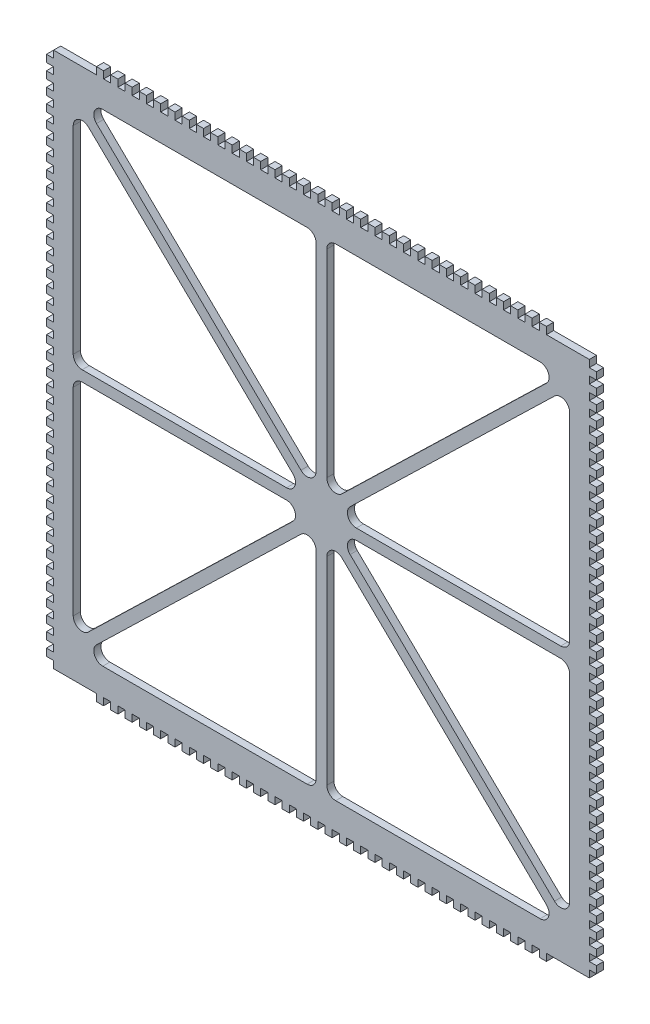
SolidWorks part; units mm, degrees
material "Cedar"
ref_plane "Front Plane" through (0, 0, 0) normal (0, 0, 1) x (1, 0, 0)
ref_plane "Top Plane" through (0, 0, 0) normal (0, 1, 0) x (1, 0, 0)
ref_plane "Right Plane" through (0, 0, 0) normal (1, 0, 0) x (0, 0, -1)
sketch "Sketch1" plane through (0, 0, 0) normal (0, 0, 1) x (1, 0, 0)
  line L0 (0, 0) -> (0, 50) construction
  line L1 (0, 0) -> (-64, 0) construction
  line L2 (-154, -150) -> (-154, 150)
  line L3 (-154, 150) -> (154, 150)
  line L5 (-122.4771, 135) -> (-8, 135)
  line L6 (5.0873, -5.1548) -> (7.1745, -3) construction
  line L7 (154, -150) -> (154, 150)
  line L8 (-154, -150) -> (154, -150)
  line L9 (3, -7.3097) -> (5.0873, -5.1548) construction
  line L10 (-130.5212, 122.4775) -> (-16.0442, 11.5914)
  line L11 (-19.5229, 3) -> (-134, 3)
  line L12 (8, 135) -> (122.4771, 135)
  line L13 (-125.9558, 126.4086) -> (-11.4788, 15.5225)
  line L14 (-3, 19.1139) -> (-3, 130)
  line L15 (64.5173, 58.544) -> (60.3428, 62.8537) construction
  line L16 (3, 130) -> (3, 19.1139)
  line L17 (11.4788, 15.5225) -> (125.9558, 126.4086)
  line L18 (62.4301, 60.6989) -> (90.4185, 87.8094) construction
  line L19 (130.5212, 122.4775) -> (16.0442, 11.5914)
  line L20 (19.5229, 3) -> (134, 3)
  line L21 (134.8255, 135) -> (136.9127, 132.8452) construction
  line L22 (136.9127, 132.8452) -> (139, 130.6903) construction
  line L23 (-76.0173, 78.0365) -> (-80.1918, 73.7268) construction
  line L24 (-80.1918, 73.7268) -> (-78.1045, 75.8817) construction
  line L25 (-78.1045, 75.8817) -> (-90.4799, 87.8689) construction
  line L26 (-134.8255, 135) -> (-136.9127, 132.8452) construction
  line L27 (-136.9127, 132.8452) -> (-139, 130.6903) construction
  line L28 (9.2327, -9.1702) -> (4.4592, -4.5465) construction
  line L29 (7.1454, -11.3251) -> (11.3199, -7.0154) construction
  line L30 (-5.0873, -5.1548) -> (-7.1745, -3) construction
  line L31 (-3, -7.3097) -> (-5.0873, -5.1548) construction
  line L32 (-10.1915, -10.099) -> (-3.6148, -3.7286) construction
  line L33 (-12.2788, -7.9441) -> (-10.1915, -10.099) construction
  line L34 (-8.1042, -12.2538) -> (-12.2788, -7.9441) construction
  line L35 (-136.9127, -132.8452) -> (-139, -130.6903) construction
  line L36 (-134.8255, -135) -> (-136.9127, -132.8452) construction
  line L37 (-80.1918, -73.7268) -> (-78.1045, -75.8817) construction
  line L38 (-76.0173, -78.0365) -> (-80.1918, -73.7268) construction
  line L39 (136.9127, -132.8452) -> (139, -130.6903) construction
  line L40 (134.8255, -135) -> (136.9127, -132.8452) construction
  line L41 (64.5173, -58.544) -> (60.3428, -62.8537) construction
  line L42 (-139, -8) -> (-139, -118.8861)
  line L43 (139, -8) -> (139, -118.8861)
  line L44 (19.5229, -3) -> (134, -3)
  line L45 (130.5212, -122.4775) -> (16.0442, -11.5914)
  line L46 (139, 8) -> (139, 118.8861)
  line L47 (-139, 8) -> (-139, 118.8861)
  line L48 (-8.1042, 12.2538) -> (-12.2788, 7.9441) construction
  line L49 (-12.2788, 7.9441) -> (-10.1915, 10.099) construction
  line L50 (-10.1915, 10.099) -> (-3.6148, 3.7286) construction
  line L51 (-3, 7.3097) -> (-5.0873, 5.1548) construction
  line L52 (-5.0873, 5.1548) -> (-7.1745, 3) construction
  line L53 (7.1454, 11.3251) -> (11.3199, 7.0154) construction
  line L54 (9.2327, 9.1702) -> (4.4592, 4.5465) construction
  line L55 (3, 7.3097) -> (5.0873, 5.1548) construction
  line L56 (5.0873, 5.1548) -> (7.1745, 3) construction
  line L57 (11.4788, -15.5225) -> (125.9558, -126.4086)
  line L58 (3, -130) -> (3, -19.1139)
  line L59 (-3, -19.1139) -> (-3, -130)
  line L60 (-125.9558, -126.4086) -> (-11.4788, -15.5225)
  line L61 (8, -135) -> (122.4771, -135)
  line L62 (-19.5229, -3) -> (-134, -3)
  line L63 (-130.5212, -122.4775) -> (-16.0442, -11.5914)
  line L64 (-122.4771, -135) -> (-8, -135)
  arc A0 (130.5212, 122.4775) -> (139, 118.8861) centre (134, 118.8861) cw
  arc A1 (134, 3) -> (139, 8) centre (134, 8) ccw
  arc A2 (16.0442, 11.5914) -> (19.5229, 3) centre (19.5229, 8) ccw
  arc A3 (3, 19.1139) -> (11.4788, 15.5225) centre (8, 19.1139) ccw
  arc A4 (125.9558, 126.4086) -> (122.4771, 135) centre (122.4771, 130) ccw
  arc A5 (3, 130) -> (8, 135) centre (8, 130) cw
  arc A6 (-125.9558, 126.4086) -> (-122.4771, 135) centre (-122.4771, 130) cw
  arc A7 (-11.4788, 15.5225) -> (-3, 19.1139) centre (-8, 19.1139) ccw
  arc A8 (-3, 130) -> (-8, 135) centre (-8, 130) ccw
  arc A9 (-16.0442, 11.5914) -> (-19.5229, 3) centre (-19.5229, 8) cw
  arc A10 (-139, 8) -> (-134, 3) centre (-134, 8) ccw
  arc A11 (-130.5212, 122.4775) -> (-139, 118.8861) centre (-134, 118.8861) ccw
  arc A12 (-130.5212, -122.4775) -> (-139, -118.8861) centre (-134, -118.8861) cw
  arc A13 (-139, -8) -> (-134, -3) centre (-134, -8) cw
  arc A14 (-16.0442, -11.5914) -> (-19.5229, -3) centre (-19.5229, -8) ccw
  arc A15 (-3, -130) -> (-8, -135) centre (-8, -130) cw
  arc A16 (-11.4788, -15.5225) -> (-3, -19.1139) centre (-8, -19.1139) cw
  arc A17 (-125.9558, -126.4086) -> (-122.4771, -135) centre (-122.4771, -130) ccw
  arc A18 (3, -130) -> (8, -135) centre (8, -130) ccw
  arc A19 (125.9558, -126.4086) -> (122.4771, -135) centre (122.4771, -130) cw
  arc A20 (3, -19.1139) -> (11.4788, -15.5225) centre (8, -19.1139) cw
  arc A21 (16.0442, -11.5914) -> (19.5229, -3) centre (19.5229, -8) cw
  arc A22 (134, -3) -> (139, -8) centre (134, -8) cw
  arc A23 (130.5212, -122.4775) -> (139, -118.8861) centre (134, -118.8861) ccw
  point P19 (0, 83)
  point P21 (0, 150)
  point P27 (-64, 0)
  point P28 (64, 0)
  point P29 (87, 0)
  point P34 (-87, 0)
  point P76 (139, 3)
  point P88 (3, 135)
  point P97 (-3, 135)
  point P103 (-139, 3)
  point P144 (-139, -3)
  point P145 (-3, -135)
  point P146 (3, -135)
  point P147 (139, -3)
  point P148 (0, -83)
  dimension "D3" = 15
  dimension "D8" = 150
  dimension "D7" = 6
  dimension "D9" = 6
  dimension "D10" = 3
  dimension "D11" = 150
  dimension "D12" = 5
  dimension "D2" = 308
  dimension "D4" = 15
  dimension "D5" = 3
  dimension "D6" = 3
  dimension "D13" = 15
extrude "Boss-Extrude1" add sketch "Sketch1" along normal blind 4
sketch "Sketch2" plane through (0, 0, 4) normal (0, 0, 1) x (1, 0, 0)
  line L0 (0, 0) -> (-89.2695, 0) construction
  line L1 (0, 0) -> (0, 71.1996) construction
  line L2 (-154, 2) -> (-150, 2)
  line L3 (-154, -150) -> (154, -150) construction
  line L4 (-154, -150) -> (-154, 150) construction
  line L5 (-154, 138) -> (-150, 138)
  line L6 (-154, 138) -> (-154, 142)
  line L7 (-154, 142) -> (-150, 142)
  line L8 (-150, 138) -> (-150, 142)
  line L9 (-154, 130) -> (-150, 130)
  line L10 (-154, 130) -> (-154, 134)
  line L11 (-154, 134) -> (-150, 134)
  line L12 (-150, 130) -> (-150, 134)
  line L13 (-154, 122) -> (-150, 122)
  line L14 (-154, 122) -> (-154, 126)
  line L15 (-154, 126) -> (-150, 126)
  line L16 (-150, 122) -> (-150, 126)
  line L17 (-154, 114) -> (-150, 114)
  line L18 (-154, 114) -> (-154, 118)
  line L19 (-154, 118) -> (-150, 118)
  line L20 (-150, 114) -> (-150, 118)
  line L21 (-154, 106) -> (-150, 106)
  line L22 (-154, 106) -> (-154, 110)
  line L23 (-154, 110) -> (-150, 110)
  line L24 (-150, 106) -> (-150, 110)
  line L25 (-154, 98) -> (-150, 98)
  line L26 (-154, 98) -> (-154, 102)
  line L27 (-154, 102) -> (-150, 102)
  line L28 (-150, 98) -> (-150, 102)
  line L29 (-154, 90) -> (-150, 90)
  line L30 (-154, 90) -> (-154, 94)
  line L31 (-154, 94) -> (-150, 94)
  line L32 (-150, 90) -> (-150, 94)
  line L33 (-154, 82) -> (-150, 82)
  line L34 (-154, 82) -> (-154, 86)
  line L35 (-154, 86) -> (-150, 86)
  line L36 (-150, 82) -> (-150, 86)
  line L37 (-154, 74) -> (-150, 74)
  line L38 (-154, 74) -> (-154, 78)
  line L39 (-154, 78) -> (-150, 78)
  line L40 (-150, 74) -> (-150, 78)
  line L41 (-154, 66) -> (-150, 66)
  line L42 (-154, 66) -> (-154, 70)
  line L43 (-154, 70) -> (-150, 70)
  line L44 (-150, 66) -> (-150, 70)
  line L45 (-154, 58) -> (-150, 58)
  line L46 (-154, 58) -> (-154, 62)
  line L47 (-154, 62) -> (-150, 62)
  line L48 (-150, 58) -> (-150, 62)
  line L49 (-154, 50) -> (-150, 50)
  line L50 (-154, 50) -> (-154, 54)
  line L51 (-154, 54) -> (-150, 54)
  line L52 (-150, 50) -> (-150, 54)
  line L53 (-154, 42) -> (-150, 42)
  line L54 (-154, 42) -> (-154, 46)
  line L55 (-154, 46) -> (-150, 46)
  line L56 (-150, 42) -> (-150, 46)
  line L57 (-154, 34) -> (-150, 34)
  line L58 (-154, 34) -> (-154, 38)
  line L59 (-154, 38) -> (-150, 38)
  line L60 (-150, 34) -> (-150, 38)
  line L61 (-154, 26) -> (-150, 26)
  line L62 (-154, 26) -> (-154, 30)
  line L63 (-154, 30) -> (-150, 30)
  line L64 (-150, 26) -> (-150, 30)
  line L65 (-154, 18) -> (-150, 18)
  line L66 (-154, 18) -> (-154, 22)
  line L67 (-154, 22) -> (-150, 22)
  line L68 (-150, 18) -> (-150, 22)
  line L69 (-154, 10) -> (-150, 10)
  line L70 (-154, 10) -> (-154, 14)
  line L71 (-154, 14) -> (-150, 14)
  line L72 (-150, 10) -> (-150, 14)
  line L73 (150, -142) -> (150, -138)
  line L74 (154, -138) -> (150, -138)
  line L75 (154, -142) -> (154, -138)
  line L76 (-150, -142) -> (-154, -142)
  line L77 (150, -134) -> (150, -130)
  line L78 (154, -130) -> (150, -130)
  line L79 (154, -134) -> (154, -130)
  line L80 (154, -134) -> (150, -134)
  line L81 (150, -126) -> (150, -122)
  line L82 (154, -122) -> (150, -122)
  line L83 (154, -126) -> (154, -122)
  line L84 (154, -126) -> (150, -126)
  line L85 (150, -118) -> (150, -114)
  line L86 (154, -114) -> (150, -114)
  line L87 (154, -118) -> (154, -114)
  line L88 (154, -118) -> (150, -118)
  line L89 (150, -110) -> (150, -106)
  line L90 (154, -106) -> (150, -106)
  line L91 (154, -110) -> (154, -106)
  line L92 (154, -110) -> (150, -110)
  line L93 (150, -102) -> (150, -98)
  line L94 (154, -98) -> (150, -98)
  line L95 (154, -102) -> (154, -98)
  line L96 (154, -102) -> (150, -102)
  line L97 (150, -94) -> (150, -90)
  line L98 (154, -90) -> (150, -90)
  line L99 (154, -94) -> (154, -90)
  line L100 (154, -94) -> (150, -94)
  line L101 (150, -86) -> (150, -82)
  line L102 (154, -82) -> (150, -82)
  line L103 (-154, 146) -> (-150, 146)
  line L104 (-154, 146) -> (-154, 150)
  line L105 (-154, 150) -> (-150, 150)
  line L106 (-150, 146) -> (-150, 150)
  line L107 (154, -86) -> (154, -82)
  line L108 (154, -86) -> (150, -86)
  line L109 (150, -78) -> (150, -74)
  line L110 (154, -74) -> (150, -74)
  line L111 (154, -78) -> (154, -74)
  line L112 (154, -78) -> (150, -78)
  line L113 (150, -70) -> (150, -66)
  line L114 (154, -66) -> (150, -66)
  line L115 (154, -70) -> (154, -66)
  line L116 (154, -70) -> (150, -70)
  line L117 (150, -62) -> (150, -58)
  line L118 (154, -58) -> (150, -58)
  line L119 (154, -62) -> (154, -58)
  line L120 (154, -62) -> (150, -62)
  line L121 (150, -54) -> (150, -50)
  line L122 (154, -50) -> (150, -50)
  line L123 (154, -54) -> (154, -50)
  line L124 (154, -54) -> (150, -54)
  line L125 (150, -46) -> (150, -42)
  line L126 (154, -42) -> (150, -42)
  line L127 (154, -46) -> (154, -42)
  line L128 (154, -46) -> (150, -46)
  line L129 (150, -38) -> (150, -34)
  line L130 (154, -34) -> (150, -34)
  line L131 (-154, 2) -> (-154, 6)
  line L132 (154, -38) -> (154, -34)
  line L133 (154, -38) -> (150, -38)
  line L134 (150, -30) -> (150, -26)
  line L135 (154, -26) -> (150, -26)
  line L136 (154, -30) -> (154, -26)
  line L137 (154, -30) -> (150, -30)
  line L138 (150, -22) -> (150, -18)
  line L139 (154, -18) -> (150, -18)
  line L140 (154, -22) -> (154, -18)
  line L141 (154, -22) -> (150, -22)
  line L142 (150, -14) -> (150, -10)
  line L143 (154, -10) -> (150, -10)
  line L144 (154, -14) -> (154, -10)
  line L145 (154, -14) -> (150, -14)
  line L146 (150, -6) -> (150, -2)
  line L147 (154, -2) -> (150, -2)
  line L148 (154, -6) -> (154, -2)
  line L149 (154, -6) -> (150, -6)
  line L150 (-154, 6) -> (-150, 6)
  line L151 (-150, 2) -> (-150, 6)
  line L152 (-154, -6) -> (-150, -6)
  line L153 (-154, -6) -> (-154, -2)
  line L154 (-154, -2) -> (-150, -2)
  line L155 (-150, -6) -> (-150, -2)
  line L156 (-154, -14) -> (-150, -14)
  line L157 (-154, -14) -> (-154, -10)
  line L158 (-154, -10) -> (-150, -10)
  line L159 (-150, -14) -> (-150, -10)
  line L160 (-154, -22) -> (-150, -22)
  line L161 (-154, -22) -> (-154, -18)
  line L162 (-154, -18) -> (-150, -18)
  line L163 (-150, -22) -> (-150, -18)
  line L164 (-154, -30) -> (-150, -30)
  line L165 (-154, -30) -> (-154, -26)
  line L166 (-154, -26) -> (-150, -26)
  line L167 (-150, -30) -> (-150, -26)
  line L168 (-154, -38) -> (-150, -38)
  line L169 (-154, -38) -> (-154, -34)
  line L170 (-154, -34) -> (-150, -34)
  line L171 (-150, -38) -> (-150, -34)
  line L172 (150, 2) -> (150, 6)
  line L173 (154, 6) -> (150, 6)
  line L174 (154, 2) -> (154, 6)
  line L175 (150, 146) -> (150, 150)
  line L176 (154, 150) -> (150, 150)
  line L177 (154, 146) -> (154, 150)
  line L178 (154, 146) -> (150, 146)
  line L179 (150, 10) -> (150, 14)
  line L180 (154, 14) -> (150, 14)
  line L181 (154, 10) -> (154, 14)
  line L182 (154, 10) -> (150, 10)
  line L183 (150, 18) -> (150, 22)
  line L184 (154, 22) -> (150, 22)
  line L185 (154, 18) -> (154, 22)
  line L186 (154, 18) -> (150, 18)
  line L187 (150, 26) -> (150, 30)
  line L188 (154, 30) -> (150, 30)
  line L189 (154, 26) -> (154, 30)
  line L190 (154, 26) -> (150, 26)
  line L191 (150, 34) -> (150, 38)
  line L192 (154, 38) -> (150, 38)
  line L193 (154, 34) -> (154, 38)
  line L194 (154, 34) -> (150, 34)
  line L195 (150, 42) -> (150, 46)
  line L196 (-154, -46) -> (-150, -46)
  line L197 (-154, -46) -> (-154, -42)
  line L198 (-154, -42) -> (-150, -42)
  line L199 (-150, -46) -> (-150, -42)
  line L200 (-154, -54) -> (-150, -54)
  line L201 (-154, -54) -> (-154, -50)
  line L202 (-154, -50) -> (-150, -50)
  line L203 (-150, -54) -> (-150, -50)
  line L204 (-154, -62) -> (-150, -62)
  line L205 (-154, -62) -> (-154, -58)
  line L206 (-154, -58) -> (-150, -58)
  line L207 (-150, -62) -> (-150, -58)
  line L208 (-154, -70) -> (-150, -70)
  line L209 (-154, -70) -> (-154, -66)
  line L210 (-154, -66) -> (-150, -66)
  line L211 (-150, -70) -> (-150, -66)
  line L212 (-154, -78) -> (-150, -78)
  line L213 (-154, -78) -> (-154, -74)
  line L214 (-154, -74) -> (-150, -74)
  line L215 (-150, -78) -> (-150, -74)
  line L216 (-154, -86) -> (-150, -86)
  line L217 (-154, -86) -> (-154, -82)
  line L218 (-154, -82) -> (-150, -82)
  line L219 (-150, -86) -> (-150, -82)
  line L220 (154, 46) -> (150, 46)
  line L221 (154, 42) -> (154, 46)
  line L222 (154, 42) -> (150, 42)
  line L223 (150, 50) -> (150, 54)
  line L224 (154, 54) -> (150, 54)
  line L225 (154, 50) -> (154, 54)
  line L226 (154, 50) -> (150, 50)
  line L227 (150, 58) -> (150, 62)
  line L228 (154, 62) -> (150, 62)
  line L229 (154, 58) -> (154, 62)
  line L230 (154, 58) -> (150, 58)
  line L231 (150, 66) -> (150, 70)
  line L232 (154, 70) -> (150, 70)
  line L233 (154, 66) -> (154, 70)
  line L234 (154, 66) -> (150, 66)
  line L235 (150, 74) -> (150, 78)
  line L236 (154, 78) -> (150, 78)
  line L237 (154, 74) -> (154, 78)
  line L238 (154, 74) -> (150, 74)
  line L239 (150, 82) -> (150, 86)
  line L240 (154, 86) -> (150, 86)
  line L241 (154, 82) -> (154, 86)
  line L242 (154, 82) -> (150, 82)
  line L243 (150, 90) -> (150, 94)
  line L244 (-154, -94) -> (-150, -94)
  line L245 (-154, -94) -> (-154, -90)
  line L246 (-154, -90) -> (-150, -90)
  line L247 (-150, -94) -> (-150, -90)
  line L248 (-154, -102) -> (-150, -102)
  line L249 (-154, -102) -> (-154, -98)
  line L250 (-154, -98) -> (-150, -98)
  line L251 (-150, -102) -> (-150, -98)
  line L252 (-154, -110) -> (-150, -110)
  line L253 (-154, -110) -> (-154, -106)
  line L254 (-154, -106) -> (-150, -106)
  line L255 (-150, -110) -> (-150, -106)
  line L256 (154, 94) -> (150, 94)
  line L257 (154, 90) -> (154, 94)
  line L258 (154, 90) -> (150, 90)
  line L259 (150, 98) -> (150, 102)
  line L260 (154, 102) -> (150, 102)
  line L261 (154, 98) -> (154, 102)
  line L262 (154, 98) -> (150, 98)
  line L263 (150, 106) -> (150, 110)
  line L264 (154, 110) -> (150, 110)
  line L265 (154, 106) -> (154, 110)
  line L266 (154, 106) -> (150, 106)
  line L267 (150, 114) -> (150, 118)
  line L268 (-154, -118) -> (-150, -118)
  line L269 (-154, -118) -> (-154, -114)
  line L270 (-154, -114) -> (-150, -114)
  line L271 (-150, -118) -> (-150, -114)
  line L272 (-154, -126) -> (-150, -126)
  line L273 (-154, -126) -> (-154, -122)
  line L274 (-154, -122) -> (-150, -122)
  line L275 (-150, -126) -> (-150, -122)
  line L276 (-154, -134) -> (-150, -134)
  line L277 (-154, -134) -> (-154, -130)
  line L278 (-154, -130) -> (-150, -130)
  line L279 (-150, -134) -> (-150, -130)
  line L280 (-154, -146) -> (-150, -146)
  line L281 (-154, -142) -> (-154, -138)
  line L282 (-154, -138) -> (-150, -138)
  line L283 (-150, -142) -> (-150, -138)
  line L284 (154, 118) -> (150, 118)
  line L285 (154, 114) -> (154, 118)
  line L286 (154, 114) -> (150, 114)
  line L287 (150, 122) -> (150, 126)
  line L288 (154, 126) -> (150, 126)
  line L289 (154, 122) -> (154, 126)
  line L290 (154, 122) -> (150, 122)
  line L291 (150, 130) -> (150, 134)
  line L292 (154, 134) -> (150, 134)
  line L293 (154, 130) -> (154, 134)
  line L294 (154, 130) -> (150, 130)
  line L295 (150, 138) -> (150, 142)
  line L296 (154, 142) -> (150, 142)
  line L297 (154, 138) -> (154, 142)
  line L298 (154, 138) -> (150, 138)
  line L299 (154, 2) -> (150, 2)
  line L300 (-154, 150) -> (154, 150) construction
  line L301 (-150, -146) -> (-150, -150)
  line L302 (-154, -150) -> (-154, -146)
  line L303 (-150, -150) -> (-154, -150)
  line L304 (150, -142) -> (154, -142)
  line L305 (150, -150) -> (154, -150)
  line L306 (150, -150) -> (150, -146)
  line L307 (150, -146) -> (154, -146)
  line L308 (154, -150) -> (154, 150) construction
  line L309 (-154, -142) -> (-150, -142) [skipped]
  line L310 (154, -146) -> (154, -150)
  dimension "D1" = 4
  dimension "D2" = 4
  dimension "D3" = 4
  dimension "D4" = 37
  dimension "D5" = 4
extrude "Cut-Extrude1" cut sketch "Sketch2" against normal blind 4
sketch "Sketch3" plane through (0, 0, 4) normal (0, 0, 1) x (1, 0, 0)
  line L0 (0, 150) -> (0, 114.5296) construction
  line L1 (-154, 150) -> (154, 150) construction
  line L2 (-10, 150) -> (-14, 150)
  line L3 (-2, 150) -> (-6, 150)
  line L4 (-2, 150) -> (-2, 154)
  line L5 (-2, 154) -> (-6, 154)
  line L6 (-6, 150) -> (-6, 154)
  line L7 (-10, 150) -> (-10, 154)
  line L8 (-10, 154) -> (-14, 154)
  line L9 (-14, 150) -> (-14, 154)
  line L10 (-18, 150) -> (-22, 150)
  line L11 (-18, 150) -> (-18, 154)
  line L12 (-18, 154) -> (-22, 154)
  line L13 (-22, 150) -> (-22, 154)
  line L14 (-26, 150) -> (-30, 150)
  line L15 (-26, 150) -> (-26, 154)
  line L16 (-26, 154) -> (-30, 154)
  line L17 (-30, 150) -> (-30, 154)
  line L18 (-34, 150) -> (-38, 150)
  line L19 (-34, 150) -> (-34, 154)
  line L20 (-34, 154) -> (-38, 154)
  line L21 (-38, 150) -> (-38, 154)
  line L22 (-42, 150) -> (-46, 150)
  line L23 (-42, 150) -> (-42, 154)
  line L24 (-42, 154) -> (-46, 154)
  line L25 (-46, 150) -> (-46, 154)
  line L26 (-50, 150) -> (-54, 150)
  line L27 (-50, 150) -> (-50, 154)
  line L28 (-50, 154) -> (-54, 154)
  line L29 (-54, 150) -> (-54, 154)
  line L30 (-58, 150) -> (-62, 150)
  line L31 (-58, 150) -> (-58, 154)
  line L32 (-58, 154) -> (-62, 154)
  line L33 (-62, 150) -> (-62, 154)
  line L34 (-66, 150) -> (-70, 150)
  line L35 (-66, 150) -> (-66, 154)
  line L36 (-66, 154) -> (-70, 154)
  line L37 (-70, 150) -> (-70, 154)
  line L38 (-74, 150) -> (-78, 150)
  line L39 (-74, 150) -> (-74, 154)
  line L40 (-74, 154) -> (-78, 154)
  line L41 (-78, 150) -> (-78, 154)
  line L42 (-82, 150) -> (-86, 150)
  line L43 (-82, 150) -> (-82, 154)
  line L44 (-82, 154) -> (-86, 154)
  line L45 (-86, 150) -> (-86, 154)
  line L46 (-90, 150) -> (-94, 150)
  line L47 (-90, 150) -> (-90, 154)
  line L48 (-90, 154) -> (-94, 154)
  line L49 (-94, 150) -> (-94, 154)
  line L50 (-98, 150) -> (-102, 150)
  line L51 (-98, 150) -> (-98, 154)
  line L52 (-98, 154) -> (-102, 154)
  line L53 (-102, 150) -> (-102, 154)
  line L54 (-106, 150) -> (-110, 150)
  line L55 (-106, 150) -> (-106, 154)
  line L56 (-106, 154) -> (-110, 154)
  line L57 (-110, 150) -> (-110, 154)
  line L58 (-114, 150) -> (-118, 150)
  line L59 (-114, 150) -> (-114, 154)
  line L60 (-114, 154) -> (-118, 154)
  line L61 (-118, 150) -> (-118, 154)
  line L62 (-122, 150) -> (-126, 150)
  line L63 (-122, 150) -> (-122, 154)
  line L64 (-122, 154) -> (-126, 154)
  line L65 (-126, 150) -> (-126, 154)
  line L66 (126, 150) -> (126, 154)
  line L67 (122, 154) -> (126, 154)
  line L68 (122, 150) -> (122, 154)
  line L69 (122, 150) -> (126, 150)
  line L70 (118, 150) -> (118, 154)
  line L71 (114, 154) -> (118, 154)
  line L72 (114, 150) -> (114, 154)
  line L73 (114, 150) -> (118, 150)
  line L74 (110, 150) -> (110, 154)
  line L75 (106, 154) -> (110, 154)
  line L76 (106, 150) -> (106, 154)
  line L77 (106, 150) -> (110, 150)
  line L78 (102, 150) -> (102, 154)
  line L79 (98, 154) -> (102, 154)
  line L80 (98, 150) -> (98, 154)
  line L81 (98, 150) -> (102, 150)
  line L82 (94, 150) -> (94, 154)
  line L83 (90, 154) -> (94, 154)
  line L84 (90, 150) -> (90, 154)
  line L85 (90, 150) -> (94, 150)
  line L86 (86, 150) -> (86, 154)
  line L87 (82, 154) -> (86, 154)
  line L88 (82, 150) -> (82, 154)
  line L89 (82, 150) -> (86, 150)
  line L90 (78, 150) -> (78, 154)
  line L91 (74, 154) -> (78, 154)
  line L92 (74, 150) -> (74, 154)
  line L93 (74, 150) -> (78, 150)
  line L94 (70, 150) -> (70, 154)
  line L95 (66, 154) -> (70, 154)
  line L96 (66, 150) -> (66, 154)
  line L97 (66, 150) -> (70, 150)
  line L98 (62, 150) -> (62, 154)
  line L99 (58, 154) -> (62, 154)
  line L100 (58, 150) -> (58, 154)
  line L101 (58, 150) -> (62, 150)
  line L102 (54, 150) -> (54, 154)
  line L103 (50, 154) -> (54, 154)
  line L104 (50, 150) -> (50, 154)
  line L105 (50, 150) -> (54, 150)
  line L106 (46, 150) -> (46, 154)
  line L107 (42, 154) -> (46, 154)
  line L108 (42, 150) -> (42, 154)
  line L109 (42, 150) -> (46, 150)
  line L110 (38, 150) -> (38, 154)
  line L111 (34, 154) -> (38, 154)
  line L112 (34, 150) -> (34, 154)
  line L113 (34, 150) -> (38, 150)
  line L114 (30, 150) -> (30, 154)
  line L115 (26, 154) -> (30, 154)
  line L116 (26, 150) -> (26, 154)
  line L117 (26, 150) -> (30, 150)
  line L118 (22, 150) -> (22, 154)
  line L119 (18, 154) -> (22, 154)
  line L120 (18, 150) -> (18, 154)
  line L121 (18, 150) -> (22, 150)
  line L122 (14, 150) -> (14, 154)
  line L123 (10, 154) -> (14, 154)
  line L124 (10, 150) -> (10, 154)
  line L125 (6, 150) -> (6, 154)
  line L126 (2, 154) -> (6, 154)
  line L127 (2, 150) -> (2, 154)
  line L128 (2, 150) -> (6, 150)
  line L129 (10, 150) -> (14, 150)
  line L130 (0, 0) -> (-64, 0) construction
  line L131 (10, -150) -> (14, -150)
  line L132 (2, -150) -> (6, -150)
  line L133 (2, -150) -> (2, -154)
  line L134 (2, -154) -> (6, -154)
  line L135 (6, -150) -> (6, -154)
  line L136 (10, -150) -> (10, -154)
  line L137 (10, -154) -> (14, -154)
  line L138 (14, -150) -> (14, -154)
  line L139 (18, -150) -> (22, -150)
  line L140 (18, -150) -> (18, -154)
  line L141 (18, -154) -> (22, -154)
  line L142 (22, -150) -> (22, -154)
  line L143 (26, -150) -> (30, -150)
  line L144 (26, -150) -> (26, -154)
  line L145 (26, -154) -> (30, -154)
  line L146 (30, -150) -> (30, -154)
  line L147 (34, -150) -> (38, -150)
  line L148 (34, -150) -> (34, -154)
  line L149 (34, -154) -> (38, -154)
  line L150 (38, -150) -> (38, -154)
  line L151 (42, -150) -> (46, -150)
  line L152 (42, -150) -> (42, -154)
  line L153 (42, -154) -> (46, -154)
  line L154 (46, -150) -> (46, -154)
  line L155 (50, -150) -> (54, -150)
  line L156 (50, -150) -> (50, -154)
  line L157 (50, -154) -> (54, -154)
  line L158 (54, -150) -> (54, -154)
  line L159 (58, -150) -> (62, -150)
  line L160 (58, -150) -> (58, -154)
  line L161 (58, -154) -> (62, -154)
  line L162 (62, -150) -> (62, -154)
  line L163 (66, -150) -> (70, -150)
  line L164 (66, -150) -> (66, -154)
  line L165 (66, -154) -> (70, -154)
  line L166 (70, -150) -> (70, -154)
  line L167 (74, -150) -> (78, -150)
  line L168 (74, -150) -> (74, -154)
  line L169 (74, -154) -> (78, -154)
  line L170 (78, -150) -> (78, -154)
  line L171 (82, -150) -> (86, -150)
  line L172 (82, -150) -> (82, -154)
  line L173 (82, -154) -> (86, -154)
  line L174 (86, -150) -> (86, -154)
  line L175 (90, -150) -> (94, -150)
  line L176 (90, -150) -> (90, -154)
  line L177 (90, -154) -> (94, -154)
  line L178 (94, -150) -> (94, -154)
  line L179 (98, -150) -> (102, -150)
  line L180 (98, -150) -> (98, -154)
  line L181 (98, -154) -> (102, -154)
  line L182 (102, -150) -> (102, -154)
  line L183 (106, -150) -> (110, -150)
  line L184 (106, -150) -> (106, -154)
  line L185 (106, -154) -> (110, -154)
  line L186 (110, -150) -> (110, -154)
  line L187 (114, -150) -> (118, -150)
  line L188 (114, -150) -> (114, -154)
  line L189 (114, -154) -> (118, -154)
  line L190 (118, -150) -> (118, -154)
  line L191 (122, -150) -> (126, -150)
  line L192 (122, -150) -> (122, -154)
  line L193 (122, -154) -> (126, -154)
  line L194 (126, -150) -> (126, -154)
  line L195 (-126, -150) -> (-126, -154)
  line L196 (-122, -154) -> (-126, -154)
  line L197 (-122, -150) -> (-122, -154)
  line L198 (-122, -150) -> (-126, -150)
  line L199 (-118, -150) -> (-118, -154)
  line L200 (-114, -154) -> (-118, -154)
  line L201 (-114, -150) -> (-114, -154)
  line L202 (-114, -150) -> (-118, -150)
  line L203 (-110, -150) -> (-110, -154)
  line L204 (-106, -154) -> (-110, -154)
  line L205 (-106, -150) -> (-106, -154)
  line L206 (-106, -150) -> (-110, -150)
  line L207 (-102, -150) -> (-102, -154)
  line L208 (-98, -154) -> (-102, -154)
  line L209 (-98, -150) -> (-98, -154)
  line L210 (-98, -150) -> (-102, -150)
  line L211 (-94, -150) -> (-94, -154)
  line L212 (-90, -154) -> (-94, -154)
  line L213 (-90, -150) -> (-90, -154)
  line L214 (-90, -150) -> (-94, -150)
  line L215 (-86, -150) -> (-86, -154)
  line L216 (-82, -154) -> (-86, -154)
  line L217 (-82, -150) -> (-82, -154)
  line L218 (-82, -150) -> (-86, -150)
  line L219 (-78, -150) -> (-78, -154)
  line L220 (-74, -154) -> (-78, -154)
  line L221 (-74, -150) -> (-74, -154)
  line L222 (-74, -150) -> (-78, -150)
  line L223 (-70, -150) -> (-70, -154)
  line L224 (-66, -154) -> (-70, -154)
  line L225 (-66, -150) -> (-66, -154)
  line L226 (-66, -150) -> (-70, -150)
  line L227 (-62, -150) -> (-62, -154)
  line L228 (-58, -154) -> (-62, -154)
  line L229 (-58, -150) -> (-58, -154)
  line L230 (-58, -150) -> (-62, -150)
  line L231 (-54, -150) -> (-54, -154)
  line L232 (-50, -154) -> (-54, -154)
  line L233 (-50, -150) -> (-50, -154)
  line L234 (-50, -150) -> (-54, -150)
  line L235 (-46, -150) -> (-46, -154)
  line L236 (-42, -154) -> (-46, -154)
  line L237 (-42, -150) -> (-42, -154)
  line L238 (-42, -150) -> (-46, -150)
  line L239 (-38, -150) -> (-38, -154)
  line L240 (-34, -154) -> (-38, -154)
  line L241 (-34, -150) -> (-34, -154)
  line L242 (-34, -150) -> (-38, -150)
  line L243 (-30, -150) -> (-30, -154)
  line L244 (-26, -154) -> (-30, -154)
  line L245 (-26, -150) -> (-26, -154)
  line L246 (-26, -150) -> (-30, -150)
  line L247 (-22, -150) -> (-22, -154)
  line L248 (-18, -154) -> (-22, -154)
  line L249 (-18, -150) -> (-18, -154)
  line L250 (-18, -150) -> (-22, -150)
  line L251 (-14, -150) -> (-14, -154)
  line L252 (-10, -154) -> (-14, -154)
  line L253 (-10, -150) -> (-10, -154)
  line L254 (-6, -150) -> (-6, -154)
  line L255 (-2, -154) -> (-6, -154)
  line L256 (-2, -150) -> (-2, -154)
  line L257 (-2, -150) -> (-6, -150)
  line L258 (-10, -150) -> (-14, -150)
  dimension "D1" = 2
  dimension "D2" = 4
  dimension "D3" = 4
  dimension "D4" = 16
extrude "Boss-Extrude2" add sketch "Sketch3" against normal blind 4
